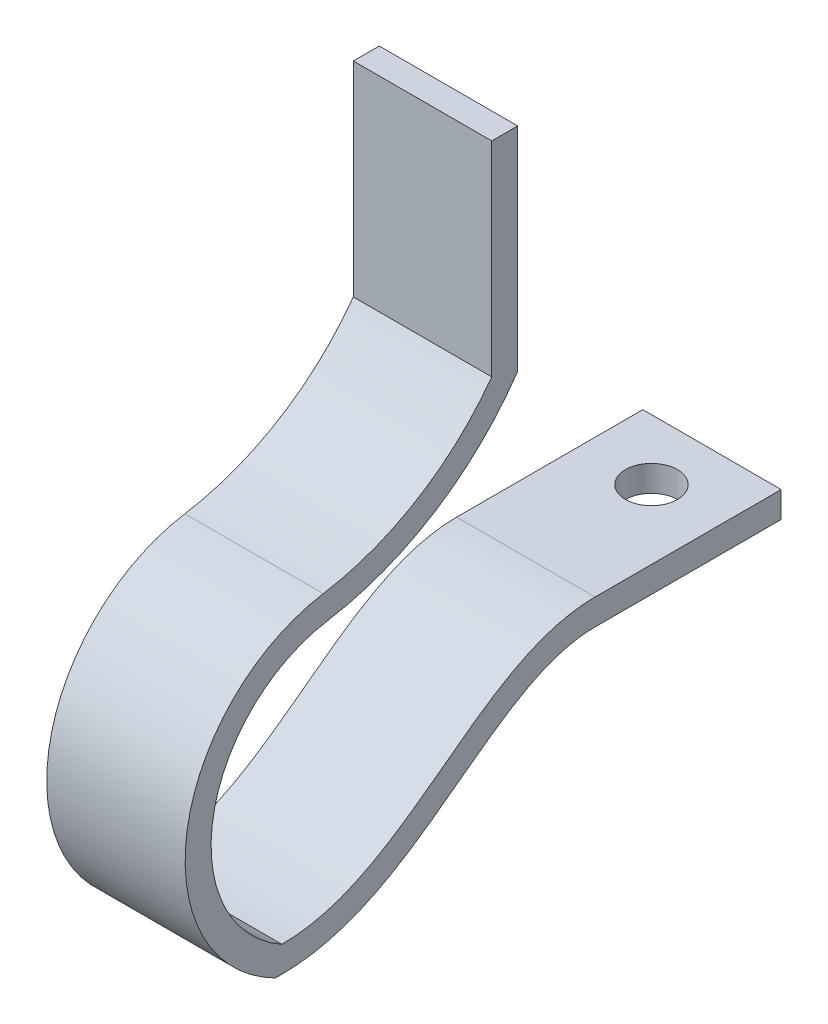
SolidWorks part; units mm, degrees
ref_plane "Front Plane" through (0, 0, 0) normal (0, 0, 1) x (1, 0, 0)
ref_plane "Top Plane" through (0, 0, 0) normal (0, 1, 0) x (1, 0, 0)
ref_plane "Right Plane" through (0, 0, 0) normal (1, 0, 0) x (0, 0, -1)
sketch "Sketch1" plane through (0, 0, 0) normal (1, 0, 0) x (0, 0, -1)
  line L2 (4.7269, -0.4448) -> (4.7269, 5.5568)
  line L3 (5.4889, -0.6861) -> (5.4889, 5.5568)
  line L4 (5.4889, 5.5568) -> (4.7269, 5.5568)
  line L7 (-1.4355, -12.5578) -> (-1.625, -12.5578)
  line L9 (7.7611, -8.3234) -> (13.2281, -8.3234)
  line L10 (13.2281, -8.3234) -> (13.2281, -7.5614)
  line L11 (13.2281, -7.5614) -> (7.6474, -7.5614)
  arc A0 (-1.625, -12.5578) -> (-0.2204, -3.4851) centre (0.5491, -8.2493) cw
  arc A1 (-0.2204, -3.4851) -> (4.7269, -0.4448) centre (-1.4354, 4.0375) ccw
  arc A3 (-0.0989, -4.2373) -> (5.4889, -0.6861) centre (-1.4354, 4.0375) ccw
  arc A4 (-1.4354, -11.7958) -> (-0.0989, -4.2373) centre (0.5491, -8.2493) cw
  arc A5 (5.1299, -9.7681) -> (-0.2204, -3.4851) centre (0.5491, -8.2493) cw construction
  arc A7 (4.4066, -9.5283) -> (-0.0989, -4.2373) centre (0.5491, -8.2493) cw construction
  spline S0 degree 3 poles (-1.4354, -11.7958) (1.6548, -11.7961) (4.0069, -8.2223) (7.2266, -7.5614) (7.7611, -7.5614) knots 0 0 0 0 0.7395 0.876252 0.876252 0.876252 0.876252
  spline S1 degree 1 poles (-1.4355, -12.5578) (7.7611, -8.3234) knots 0 0 1 1 construction
  spline S2 degree 3 poles (-1.4355, -12.5578) (-1.1759, -12.5578) (-0.6489, -12.5194) (0.3261, -12.3089) (1.4402, -11.8417) (2.6269, -11.0966) (4.0803, -10.0111) (5.7692, -8.7469) (7.0661, -8.3234) (7.7611, -8.3234) knots 0 0 0 0 0.054766 0.109532 0.219063 0.328595 0.438126 0.657189 0.876252 0.876252 0.876252 0.876252
  dimension "D1" = 0.762
  dimension "D3" = 7.62
  dimension "D4" = 0.762
extrude "Boss-Extrude1" add sketch "Sketch1" against normal blind 4.064
ref_plane "Plane1" through (-2.032, 0, 0) normal (1, 0, 0) x (0, 0, -1)
sketch "Sketch2" plane through (0, -7.5614, 0) normal (0, 1, 0) x (1, 0, 0)
  line L0 (-4.064, 13.2281) -> (0, 13.2281) construction
  circle A0 centre (-2.032, 11.4501) radius 0.762
  point P4 (0, 0)
  point P5 (-2.032, 13.2281)
  dimension "D1" = 1.524
  dimension "D2" = 1.778
extrude "Cut-Extrude1" cut sketch "Sketch2" against normal through all
